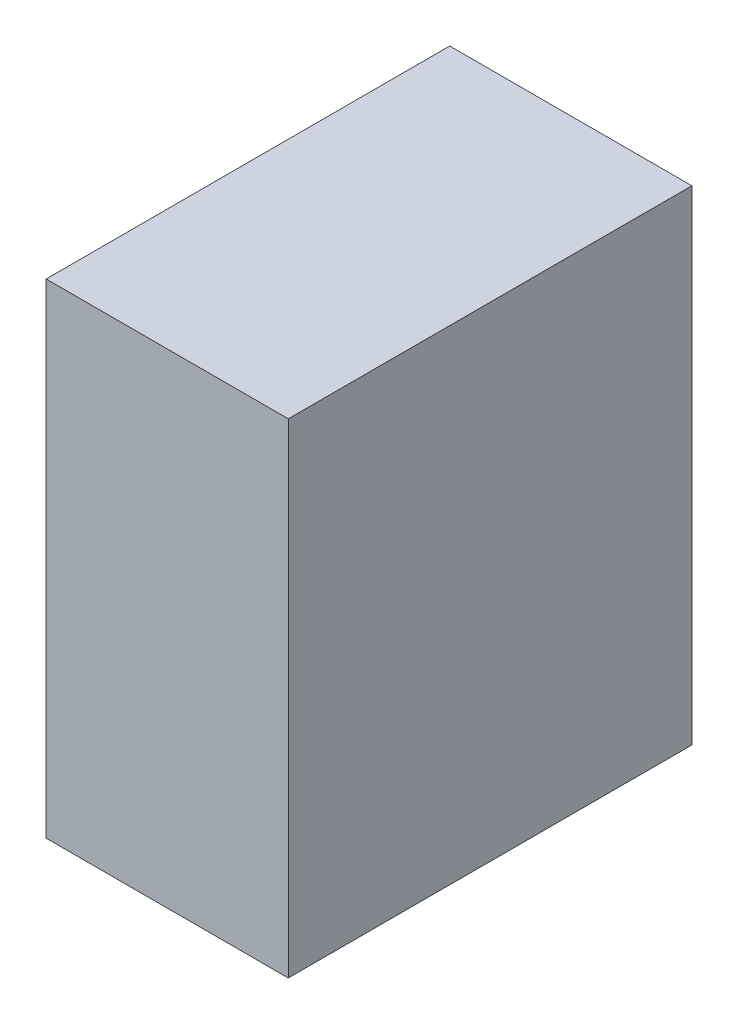
SolidWorks part; units mm, degrees
ref_plane "Front Plane" through (0, 0, 0) normal (0, 0, 1) x (1, 0, 0)
ref_plane "Top Plane" through (0, 0, 0) normal (0, 1, 0) x (1, 0, 0)
ref_plane "Right Plane" through (0, 0, 0) normal (1, 0, 0) x (0, 0, -1)
sketch "Sketch1" plane through (0, 0, 0) normal (0, 1, 0) x (1, 0, 0)
  line L1 (-38.1, 63.5) -> (38.1, 63.5)
  line L2 (-38.1, 63.5) -> (-38.1, -63.5)
  line L3 (-38.1, -63.5) -> (38.1, -63.5)
  line L4 (38.1, 63.5) -> (38.1, -63.5)
  line L5 (-38.1, 63.5) -> (38.1, -63.5) construction
  line L6 (-38.1, -63.5) -> (38.1, 63.5) construction
  point P0 (0, 0)
  dimension "D1" = 127
  dimension "D2" = 76.2
extrude "Boss-Extrude1" add sketch "Sketch1" along normal blind 152.4
